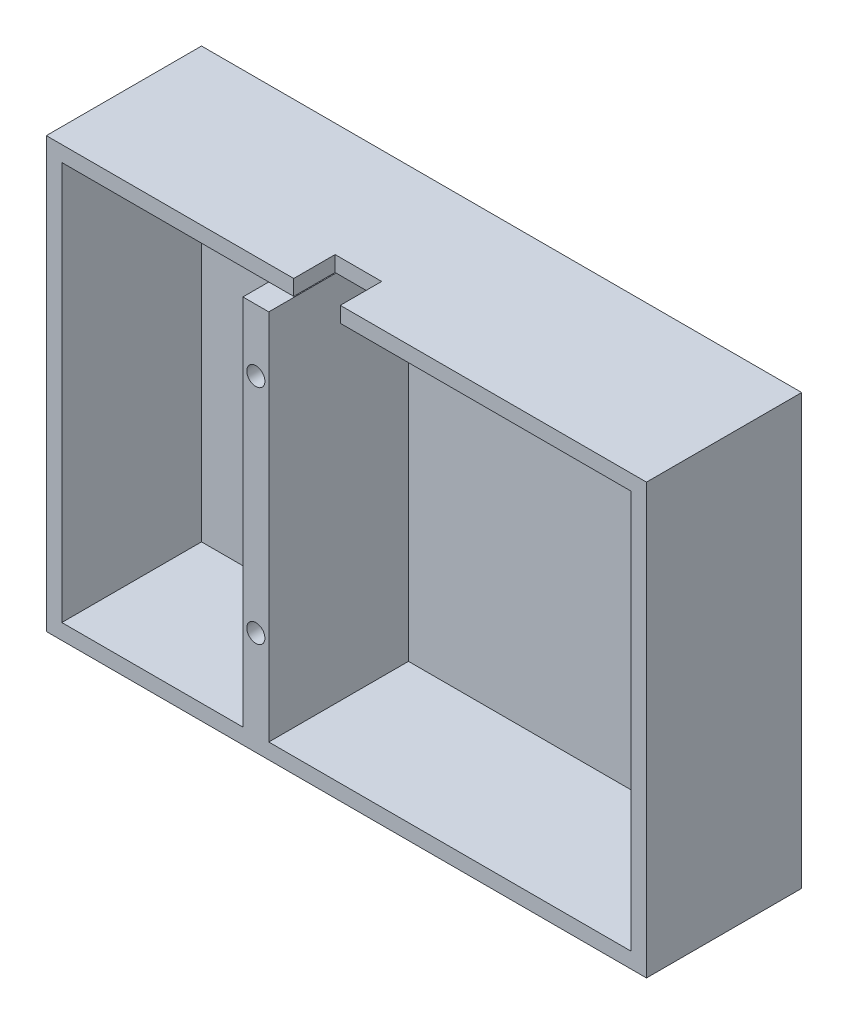
SolidWorks part; units mm, degrees
ref_plane "Front Plane" through (0, 0, 0) normal (0, 0, 1) x (1, 0, 0)
ref_plane "Top Plane" through (0, 0, 0) normal (0, 1, 0) x (1, 0, 0)
ref_plane "Right Plane" through (0, 0, 0) normal (1, 0, 0) x (0, 0, -1)
sketch "Sketch1" plane through (0, 0, 0) normal (0, 0, 1) x (1, 0, 0)
  line L1 (-73, 80) -> (-3, 80)
  line L2 (-73, 80) -> (-73, 3)
  line L3 (-73, 3) -> (-3, 3)
  line L4 (-3, 80) -> (-3, 3)
  line L5 (-113, 80) -> (-78, 80)
  line L6 (-113, 80) -> (-113, 3)
  line L7 (-113, 3) -> (-78, 3)
  line L8 (-78, 80) -> (-78, 3)
  line L9 (-116, 83) -> (0, 83)
  line L10 (-116, 83) -> (-116, 0)
  line L11 (-116, 0) -> (0, 0)
  line L12 (0, 83) -> (0, 0)
  dimension "D1" = 77
  dimension "D2" = 70
  dimension "D3" = 35
  dimension "D4" = 77
  dimension "D5" = 5
  dimension "D6" = 3
  dimension "D7" = 3
  dimension "D8" = 3
  dimension "D9" = 3
extrude "Boss-Extrude1" add sketch "Sketch1" along normal blind 30
sketch "Sketch2" plane through (0, 0, 0) normal (0, 0, -1) x (-1, 0, 0)
  line L0 (3, 3) -> (3, 80) construction
  line L1 (3, 80) -> (73, 80) construction
  line L2 (73, 80) -> (73, 3) construction
  line L3 (73, 3) -> (3, 3) construction
  line L4 (113, 3) -> (78, 3) construction
  line L5 (78, 3) -> (78, 80) construction
  line L6 (113, 80) -> (113, 3) construction
  line L7 (78, 80) -> (113, 80) construction
  line L8 (3, 3) -> (3, 80)
  line L9 (3, 80) -> (73, 80)
  line L10 (73, 80) -> (73, 3)
  line L11 (73, 3) -> (3, 3)
  line L12 (113, 3) -> (78, 3)
  line L13 (78, 3) -> (78, 80)
  line L14 (113, 80) -> (113, 3)
  line L15 (78, 80) -> (113, 80)
extrude "Boss-Extrude2" add sketch "Sketch2" against normal blind 3
sketch "Sketch3" plane through (-73, 0, 0) normal (1, 0, 0) x (0, 0, -1)
  line L0 (-30, 80) -> (-30, 3) construction
  line L1 (-30, 75) -> (-3, 75)
  line L2 (-30, 75) -> (-30, 80)
  line L3 (-30, 80) -> (-3, 80)
  line L4 (-3, 75) -> (-3, 80)
  line L5 (-3, 3) -> (-3, 80) construction
  line L6 (-30, 80) -> (-3, 80) construction
  point P8 (-30, 77.5)
  dimension "D1" = 5
  dimension "D2" = 0
extrude "Cut-Extrude1" cut sketch "Sketch3" against normal blind 5
sketch "Sketch5" plane through (0, 0, 0) normal (0, -1, 0) x (-1, 0, 0)
  line L0 (116, 0) -> (0, 0) construction
  line L1 (0, -30) -> (0, 0) construction
  circle A0 centre (12.5, -8) radius 5
  dimension "D1" = 10
  dimension "D2" = 8
  dimension "D3" = 12.5
extrude "Cut-Extrude3" cut sketch "Sketch5" against normal blind 10
sketch "Sketch6" plane through (0, 0, 30) normal (0, 0, 1) x (1, 0, 0)
  line L0 (0, 83) -> (-116, 83) construction
  line L1 (0, 0) -> (0, 83) construction
  line L4 (-116, 0) -> (0, 0) construction
  circle A0 centre (-75.5, 63) radius 1.75
  circle A1 centre (-75.5, 20) radius 1.75
  dimension "D4" = 3.5
  dimension "D5" = 3.5
  dimension "D1" = 20
  dimension "D2" = 20
  dimension "D3" = 75.5
extrude "Cut-Extrude4" cut sketch "Sketch6" against normal blind 30
sketch "Sketch7" plane through (0, 83, 0) normal (0, 1, 0) x (1, 0, 0)
  line L0 (-68.1822, -30) -> (-68.1822, -22)
  line L1 (0, -30) -> (-116, -30) construction
  line L2 (-68.1822, -22) -> (-67.1159, -22.6647)
  line L3 (-68.1822, -22) -> (-59.1822, -22)
  line L4 (-59.1822, -22) -> (-59.1822, -30)
  line L5 (-59.1822, -30) -> (-68.1822, -30)
extrude "Cut-Extrude5" cut sketch "Sketch7" against normal blind 10
